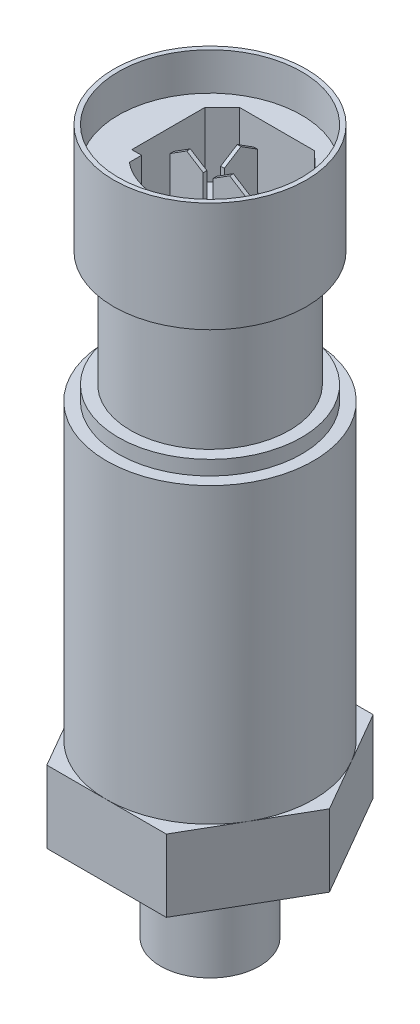
SolidWorks part; units mm, degrees
ref_plane "Front Plane" through (0, 0, 0) normal (0, 0, 1) x (1, 0, 0)
ref_plane "Top Plane" through (0, 0, 0) normal (0, 1, 0) x (1, 0, 0)
ref_plane "Right Plane" through (0, 0, 0) normal (1, 0, 0) x (0, 0, -1)
sketch "Sketch1" plane through (0, 0, 0) normal (0, 1, 0) x (1, 0, 0)
  circle A0 centre (0, 0) radius 5.1435
  dimension "D1" = 10.287
extrude "Boss-Extrude1" add sketch "Sketch1" along normal blind 10.3
sketch "Sketch2" plane through (0, 10.3, 0) normal (0, 1, 0) x (1, 0, 0)
  line L1 (6.2065, 10.75) -> (-6.2065, 10.75)
  line L2 (-6.2065, 10.75) -> (-12.413, 0)
  line L3 (-12.413, 0) -> (-6.2065, -10.75)
  line L4 (-6.2065, -10.75) -> (6.2065, -10.75)
  line L5 (6.2065, -10.75) -> (12.413, 0)
  line L6 (12.413, 0) -> (6.2065, 10.75)
  circle A0 centre (0, 0) radius 10.75 construction
  dimension "D1" = 21.5
  dimension "D2" = 21.5
extrude "Boss-Extrude2" add sketch "Sketch2" along normal blind 7.5
sketch "Sketch3" plane through (0, 17.8, 0) normal (0, 1, 0) x (1, 0, 0)
  circle A0 centre (0, 0) radius 10.75
extrude "Boss-Extrude3" add sketch "Sketch3" along normal blind 30.48
sketch "Sketch4" plane through (0, 48.28, 0) normal (0, 1, 0) x (1, 0, 0)
  circle A0 centre (0, 0) radius 9.525
  dimension "D1" = 19.05
extrude "Boss-Extrude4" add sketch "Sketch4" along normal blind 1.5
sketch "Sketch5" plane through (0, 49.78, 0) normal (0, 1, 0) x (1, 0, 0)
  circle A1 centre (0, 0) radius 8.255
  dimension "D1" = 16.51
extrude "Boss-Extrude5" add sketch "Sketch5" along normal blind 12
sketch "Sketch6" plane through (0, 61.78, 0) normal (0, 1, 0) x (1, 0, 0)
  circle A0 centre (0, 0) radius 10
  dimension "D1" = 20
extrude "Boss-Extrude6" add sketch "Sketch6" along normal blind 11.4
sketch "Sketch7" plane through (0, 0, 0) normal (0, -1, 0) x (1, 0, 0)
  circle A0 centre (0, 0) radius 4.3053
  dimension "D1" = 8.6106
extrude "Cut-Extrude1" cut sketch "Sketch7" against normal blind 11.4
thread "Thread1" pitch 1.0583 start angle 0, offset 0, length 0, pitch 0.9408, diameter 10.287
ref_plane "Plane1" through (5.1435, 0, 0) normal (0, 0, 1) x (1, 0, 0)
sketch "Thread Profile1" plane through (5.1435, 0, 0) normal (0, 0, 1) x (1, 0, 0)
  line L0 (0, 0) -> (0, 1.0583) construction
  line L11 (0, 0) -> (0, 0.926)
  line L12 (0, 0.926) -> (-0.5728, 0.5953)
  line L13 (-0.5728, 0.5953) -> (-0.5728, 0.3307)
  line L15 (-0.5728, 0.3307) -> (0, 0)
  line L17 (-0.5728, 0.463) -> (0, 0.463) construction
  point P2 (0, 0)
  dimension "Pitch" = 1.0583
  dimension "Profile_Angle" = 60
  dimension "Profile_Land" = 0.2646
  dimension "Profile_Height" = 0.5728
sketch "Sketch28" plane through (0, 0, 0) normal (0, -1, 0) x (-1, 0, 0)
  circle A0 centre (0, 0) radius 4.3053
extrude "Boss-Extrude7" add sketch "Sketch28" against normal blind 11.4
sketch "Sketch29" plane through (0, 0, 0) normal (0, -1, 0) x (1, 0, 0)
  circle A0 centre (0, 0) radius 1.5
  dimension "D1" = 3
extrude "Cut-Extrude2" cut sketch "Sketch29" against normal blind 11.4 contours A0
sketch "Sketch30" plane through (0, 73.18, 0) normal (0, 1, 0) x (1, 0, 0)
  circle A0 centre (0, 0) radius 9.525
  dimension "D1" = 19.05
extrude "Cut-Extrude6" cut sketch "Sketch30" against normal blind 10.638
sketch "Sketch31" plane through (0, 62.542, 0) normal (0, 1, 0) x (1, 0, 0)
  line L1 (0, 16.67) -> (0, -21.3304) construction
  line L2 (0, -21.3304) -> (0, 0) construction
  line L3 (0, 0) -> (26.7846, 0) construction
  line L4 (26.7846, 0) -> (-26.2213, 0) construction
  line L5 (-0.1905, 4.7444) -> (0.1905, 4.7444)
  line L6 (-0.1905, 4.7444) -> (-0.1905, 1.3008)
  line L7 (-0.1905, 1.3008) -> (0.1905, 1.3008)
  line L8 (0.1905, 4.7444) -> (0.1905, 1.3008)
  line L9 (-0.1905, 4.7444) -> (0.1905, 1.3008) construction
  line L10 (-0.1905, 1.3008) -> (0.1905, 4.7444) construction
  line L11 (-3.957, 0.1905) -> (-0.5134, 0.1905)
  line L12 (-3.957, 0.1905) -> (-3.957, -0.1905)
  line L13 (-3.957, -0.1905) -> (-0.5134, -0.1905)
  line L14 (-0.5134, 0.1905) -> (-0.5134, -0.1905)
  line L15 (-3.957, 0.1905) -> (-0.5134, -0.1905) construction
  line L16 (-3.957, -0.1905) -> (-0.5134, 0.1905) construction
  line L17 (0.5134, 0.1905) -> (3.957, 0.1905)
  line L18 (0.5134, 0.1905) -> (0.5134, -0.1905)
  line L19 (0.5134, -0.1905) -> (3.957, -0.1905)
  line L20 (3.957, 0.1905) -> (3.957, -0.1905)
  line L21 (0.5134, 0.1905) -> (3.957, -0.1905) construction
  line L22 (0.5134, -0.1905) -> (3.957, 0.1905) construction
  circle A0 centre (0, 0) radius 10 construction
  circle A1 centre (0, 0) radius 9.525 construction
  circle A3 centre (0, 0) radius 9.525 construction
  point P3 (0, 3.0226)
  point P11 (-2.2352, 0)
  point P16 (2.2352, 0)
  dimension "D1" = 0.381
  dimension "D2" = 0.381
  dimension "D3" = 0.381
  dimension "D4" = 2.2352
  dimension "D5" = 2.2352
  dimension "D6" = 3.0226
  dimension "D7" = 3.957
  dimension "D8" = 0.1905
  dimension "D9" = 4.7444
extrude "Boss-Extrude8" add sketch "Sketch31" along normal blind 7.239
sketch "Sketch32" plane through (0, 0, 0.1905) normal (0, 0, 1) x (1, 0, 0)
  line L0 (-2.2352, 69.781) -> (-0.5134, 68.6888) construction
  line L1 (-3.957, 69.781) -> (-0.5134, 69.781) construction
  line L2 (-0.5134, 69.781) -> (-0.5134, 62.542) construction
  line L3 (-0.5134, 68.6888) -> (-3.957, 68.6888) construction
  line L4 (-3.957, 69.781) -> (-3.957, 62.542) construction
  line L5 (-3.957, 68.6888) -> (-2.2352, 69.781) construction
  line L6 (-2.2352, 69.781) -> (-3.957, 68.6888)
  line L7 (-3.957, 68.6888) -> (-0.5134, 68.6888)
  line L8 (-0.5134, 68.6888) -> (-2.2352, 69.781)
  line L10 (-3.957, 62.542) -> (-0.5134, 62.542)
  line L11 (-0.5134, 62.542) -> (-0.5134, 69.781)
  line L12 (-0.5134, 69.781) -> (-3.957, 69.781)
  line L13 (-3.957, 69.781) -> (-3.957, 62.542)
  line L14 (-3.957, 62.542) -> (-0.5134, 62.542)
  line L15 (-0.5134, 62.542) -> (-0.5134, 69.781)
  line L16 (-0.5134, 69.781) -> (-3.957, 69.781)
  line L17 (-3.957, 69.781) -> (-3.957, 62.542)
  line M7 (-0.5134, 62.542) -> (-0.5134, 69.781)
  line M8 (-0.5134, 69.781) -> (-3.957, 69.781)
  line M9 (-3.957, 69.781) -> (-3.957, 62.542)
  dimension "D1" = 1.0922
  dimension "D2" = 0
extrude "Cut-Extrude7" cut sketch "Sketch32" against normal blind 6.731 contours L6 M8 M9 | L8 M7 M8
sketch "Sketch33" plane through (0, 0, 0.1905) normal (0, 0, 1) x (1, 0, 0)
  line L0 (2.2352, 69.781) -> (3.957, 68.6888) construction
  line L1 (0.5134, 69.781) -> (3.957, 69.781) construction
  line L2 (3.957, 69.781) -> (3.957, 62.542) construction
  line L3 (3.957, 68.6888) -> (0.5134, 68.6888) construction
  line L4 (0.5134, 69.781) -> (0.5134, 62.542) construction
  line L5 (0.5134, 68.6888) -> (2.2352, 69.781) construction
  line L6 (2.2352, 69.781) -> (3.957, 68.6888)
  line L7 (3.957, 68.6888) -> (0.5134, 68.6888)
  line L8 (0.5134, 68.6888) -> (2.2352, 69.781)
  line L13 (0.5134, 62.542) -> (3.957, 62.542)
  line L14 (3.957, 62.542) -> (3.957, 69.781)
  line L15 (3.957, 69.781) -> (0.5134, 69.781)
  line L16 (0.5134, 69.781) -> (0.5134, 62.542)
  line L17 (0.5134, 62.542) -> (3.957, 62.542)
  line L18 (3.957, 62.542) -> (3.957, 69.781)
  line L19 (3.957, 69.781) -> (0.5134, 69.781)
  line L20 (0.5134, 69.781) -> (0.5134, 62.542)
  line M10 (3.957, 62.542) -> (3.957, 69.781)
  line M11 (3.957, 69.781) -> (0.5134, 69.781)
  line M12 (0.5134, 69.781) -> (0.5134, 62.542)
  dimension "D1" = 1.0922
  dimension "D2" = 0
extrude "Cut-Extrude8" cut sketch "Sketch33" against normal blind 1.651 contours L8 M12 M11 | L6 M11 M10
sketch "Sketch34" plane through (0.1905, 0, 0) normal (1, 0, 0) x (0, 0, -1)
  line L0 (3.0226, 69.781) -> (4.7444, 68.6888)
  line L1 (1.3008, 69.781) -> (4.7444, 69.781) construction
  line L2 (4.7444, 69.781) -> (4.7444, 62.542) construction
  line L3 (4.7444, 68.6888) -> (1.3008, 68.6888)
  line L4 (1.3008, 69.781) -> (1.3008, 62.542) construction
  line L5 (1.3008, 68.6888) -> (3.0226, 69.781)
  line L10 (1.3008, 62.542) -> (4.7444, 62.542)
  line L11 (4.7444, 62.542) -> (4.7444, 69.781)
  line L12 (4.7444, 69.781) -> (1.3008, 69.781)
  line L13 (1.3008, 69.781) -> (1.3008, 62.542)
  line L14 (1.3008, 62.542) -> (4.7444, 62.542)
  line L15 (4.7444, 62.542) -> (4.7444, 69.781)
  line L16 (4.7444, 69.781) -> (1.3008, 69.781)
  line L17 (1.3008, 69.781) -> (1.3008, 62.542)
  line M9 (4.7444, 62.542) -> (4.7444, 69.781)
  line M10 (4.7444, 69.781) -> (1.3008, 69.781)
  line M11 (1.3008, 69.781) -> (1.3008, 62.542)
  dimension "D1" = 1.0922
  dimension "D2" = 0
extrude "Cut-Extrude9" cut sketch "Sketch34" against normal blind 1.651 contours L5 M11 M10 | L0 M10 M9
sketch "Sketch35" plane through (0, 62.542, 0) normal (0, 1, 0) x (1, 0, 0)
  line L0 (-3.9189, 6.985) -> (-5.715, 5.1889)
  line L1 (3.0134, -3.683) -> (4.3631, -3.683)
  line L2 (-5.715, -2.413) -> (-5.715, 5.1889)
  line L3 (-3.9189, 6.985) -> (3.8604, 6.985)
  line L4 (5.715, -2.413) -> (5.715, 5.2423)
  line L5 (-4.699, -5.7432) -> (4.9089, 5.9998) construction
  line L6 (-4.9068, 5.9972) -> (4.3631, -5.3326) construction
  line L7 (3.8604, 6.985) -> (5.715, 5.2423)
  line L8 (-5.715, -2.413) -> (-4.699, -2.413)
  line L9 (-4.699, -2.413) -> (-4.699, -3.683)
  line L10 (5.715, -2.413) -> (4.3631, -2.413)
  line L11 (4.3631, -2.413) -> (4.3631, -3.683)
  arc A0 (-4.699, -3.683) -> (4.3631, -3.683) centre (-0.168, 1.7488) ccw
  circle A1 centre (0, 0) radius 9.525
  circle A2 centre (0, 0) radius 9.525
  circle A3 centre (0, 0) radius 10.75 construction
  point P0 (0, 0)
  circle M12 centre (0, 0) radius 9.525
  dimension "D15" = 1.7568
  dimension "D16" = 7.0735
  dimension "D2" = 7.6019
  dimension "D3" = 7.7487
  dimension "D4" = 5.9998
  dimension "D5" = 6.985
  dimension "D6" = 1.27
  dimension "D7" = 1.016
  dimension "D8" = 1.3519
  dimension "D9" = 9.0621
  dimension "D10" = 2.54
  dimension "D11" = 2.5449
  dimension "D12" = 7.6553
  dimension "D13" = 3.683
  dimension "D14" = 5.715
  dimension "D1" = 0
extrude "Boss-Extrude9" add sketch "Sketch35" along normal blind 6.731 contours A0 L9 L8 L2 L0 L3 L7 L4 L10 L11 M12
